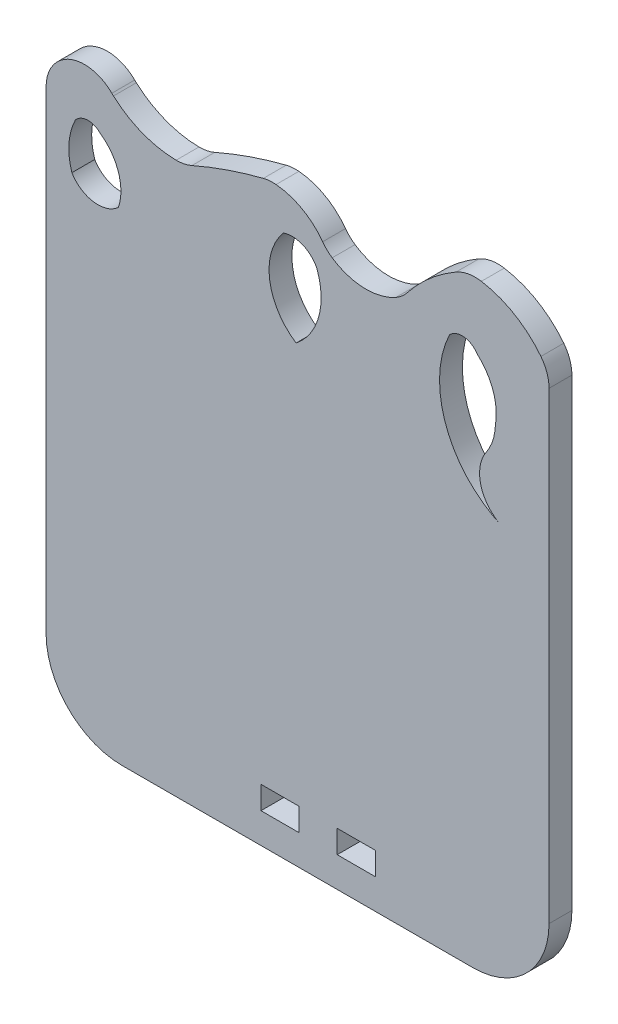
SolidWorks part; units mm, degrees
ref_plane "Alzado" through (0, 0, 0) normal (0, 0, 1) x (1, 0, 0)
ref_plane "Planta" through (0, 0, 0) normal (0, 1, 0) x (1, 0, 0)
ref_plane "Vista lateral" through (0, 0, 0) normal (1, 0, 0) x (0, 0, -1)
sketch "Model" plane through (0, 0, 0) normal (0, 0, 1) x (1, 0, 0)
  line L0 (4.976, 40.4253) -> (4.976, -2.8132)
  line L1 (4.976, 49.8845) -> (4.976, 40.4253)
  line L2 (70.979, -5.4306) -> (70.9821, -10.4306)
  line L3 (4.976, -12.3158) -> (4.976, -2.8132)
  line L4 (60.9878, -22.27) -> (14.9857, -22.3158)
  line L5 (70.976, 48.5694) -> (70.976, -12.27)
  line L6 (43.176, -15.3354) -> (43.176, -18.3354)
  line L7 (48.176, -15.3354) -> (43.176, -15.3354)
  line L8 (48.176, -18.3354) -> (48.176, -15.3354)
  line L9 (43.176, -18.3354) -> (48.176, -18.3354)
  line L10 (33.176, -15.3354) -> (33.176, -18.3354)
  line L11 (38.176, -15.3354) -> (33.176, -15.3354)
  line L12 (38.176, -18.3354) -> (38.176, -15.3354)
  line L13 (33.176, -18.3354) -> (38.176, -18.3354)
  arc A0 (57.9187, 48.1328) -> (64.9073, 29.7614) centre (70.2246, 42.2991) ccw
  arc A1 (62.7308, 37.1847) -> (64.9073, 29.7614) centre (66.8595, 34.3645) ccw
  arc A2 (62.7308, 37.1847) -> (63.9362, 40.8809) centre (57.0029, 41.0973) ccw
  arc A3 (63.9362, 40.8809) -> (61.5446, 47.7471) centre (56.6325, 42.1866) ccw
  arc A4 (61.5446, 47.7471) -> (57.9187, 48.1328) centre (59.5808, 46.5224) ccw
  arc A5 (36.1295, 48.7913) -> (37.7837, 37.1196) centre (42.0623, 43.6791) ccw
  arc A6 (40.4905, 46.9989) -> (36.1295, 48.7913) centre (37.2801, 45.3892) ccw
  arc A7 (37.7837, 37.1196) -> (40.4905, 46.9989) centre (32.4524, 43.8908) ccw
  arc A8 (8.8241, 47.9942) -> (8.359, 41.7624) centre (16.2093, 44.3098) ccw
  arc A9 (12.0485, 48.1182) -> (8.8241, 47.9942) centre (10.4928, 46.5857) ccw
  arc A10 (14.4668, 40.8632) -> (12.0485, 48.1182) centre (8.4203, 42.8783) ccw
  arc A11 (8.359, 41.7624) -> (14.4668, 40.8632) centre (11.7832, 43.8282) ccw
  arc A12 (4.976, -12.3158) -> (14.9857, -22.3158) centre (14.976, -12.3158) ccw
  arc A13 (60.9878, -22.27) -> (70.976, -12.27) centre (60.976, -12.27) ccw
  arc A14 (70.976, 48.5694) -> (69.9082, 51.6576) centre (65.976, 48.5694) ccw
  arc A15 (69.9082, 51.6576) -> (62.0976, 56.2855) centre (60.0397, 43.9072) ccw
  arc A16 (62.0976, 56.2855) -> (58.7766, 55.6828) centre (61.2776, 51.3532) ccw
  arc A17 (58.7766, 55.6828) -> (52.3528, 50.113) centre (70.0068, 36.2413) ccw
  arc A18 (50.89, 48.8542) -> (52.3528, 50.113) centre (48.4213, 53.2022) ccw
  arc A19 (42.5169, 49.1673) -> (50.89, 48.8542) centre (46.9567, 55.7819) ccw
  arc A20 (41.2679, 50.3669) -> (42.5169, 49.1673) centre (45.3034, 53.3189) ccw
  arc A21 (13.6013, 53.4124) -> (4.976, 49.8845) centre (10.0253, 49.8474) ccw
  arc A22 (13.6013, 53.4124) -> (13.8158, 53.2096) centre (17.1424, 56.9424) ccw
  arc A23 (13.8158, 53.2096) -> (22.0425, 50.0252) centre (22.1775, 62.5926) ccw
  arc A24 (22.0425, 50.0252) -> (24.1102, 50.4484) centre (22.0962, 55.0249) ccw
  arc A25 (33.4829, 53.6791) -> (24.1102, 50.4484) centre (48.2989, -4.5156) ccw
  arc A26 (35.1546, 53.8145) -> (33.4829, 53.6791) centre (34.7165, 48.8337) ccw
  arc A27 (41.2679, 50.3669) -> (35.1546, 53.8145) centre (34.4101, 45.3505) ccw
extrude "Saliente-Extruir1" add sketch "Model" along normal blind 3 contours A20 A27 A26 A25 A24 A23 A22 A21 L1 L0 L3 A12 L4 A13 L5 A14 A15 A16 A17 A18 A19 L9 L6 L7 L8 L13 L10 L11 L12 A4 A3 A2 A1 A0 A7 A5 A6 A11 A8 A9 A10
